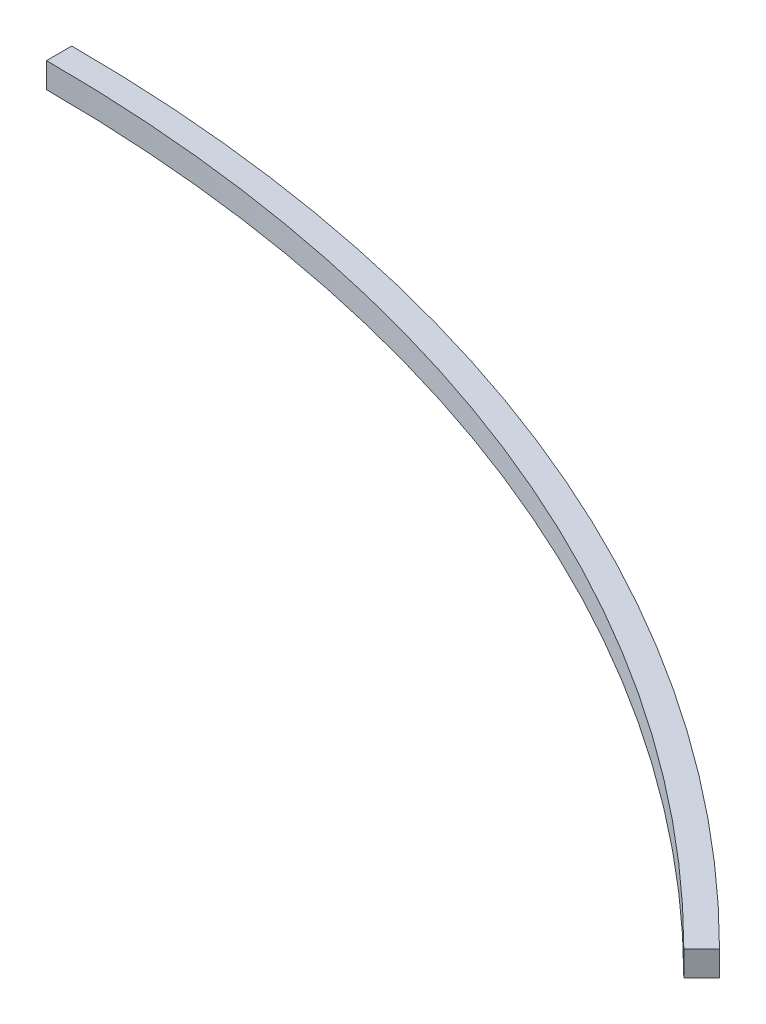
SolidWorks part; units mm, degrees
ref_plane "Front Plane" through (0, 0, 0) normal (0, 0, 1) x (1, 0, 0)
ref_plane "Top Plane" through (0, 0, 0) normal (0, 1, 0) x (1, 0, 0)
ref_plane "Right Plane" through (0, 0, 0) normal (1, 0, 0) x (0, 0, -1)
sketch "Sketch1" plane through (0, 0, 0) normal (0, 1, 0) x (1, 0, 0)
  line L0 (0, 0) -> (0, 610) construction
  line L1 (0, 610) -> (0, 620)
  line L2 (0, 0) -> (438.4062, 438.4062) construction
  line L3 (431.3351, 431.3351) -> (438.4062, 438.4062)
  arc A0 (0, 610) -> (431.3351, 431.3351) centre (0, 0) cw
  arc A1 (0, 620) -> (438.4062, 438.4062) centre (0, 0) cw
  dimension "D1" = 610
  dimension "D2" = 10
  dimension "D3" = 45
  dimension "D4" = 620
extrude "Boss-Extrude1" add sketch "Sketch1" along normal blind 10 contours A1 L1 A0 L3
